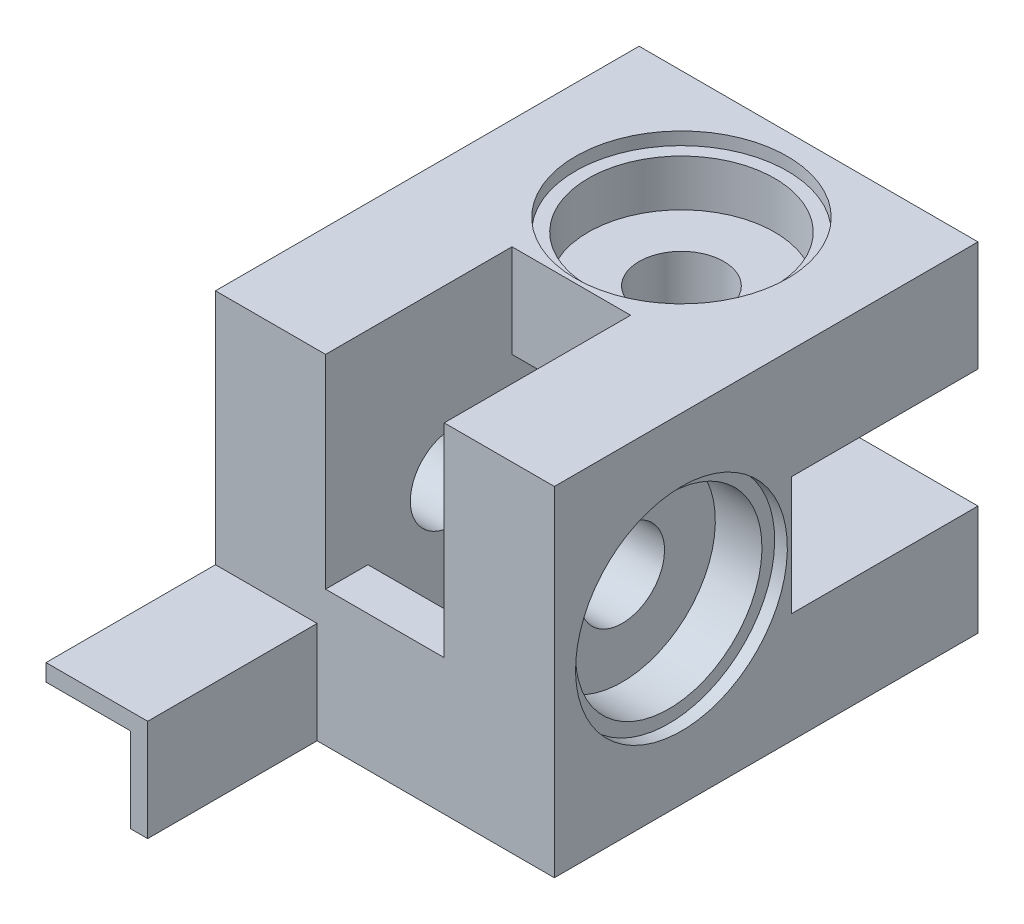
SolidWorks part; units mm, degrees
ref_plane "Plan de face" through (0, 0, 0) normal (0, 0, 1) x (1, 0, 0)
ref_plane "Plan de dessus" through (0, 0, 0) normal (0, 1, 0) x (1, 0, 0)
ref_plane "Plan de droite" through (0, 0, 0) normal (1, 0, 0) x (0, 0, -1)
sketch "Esquisse1" plane through (0, 0, 0) normal (0, 0, 1) x (1, 0, 0)
  line L1 (-40, 40) -> (0, 40)
  line L2 (-40, 40) -> (-40, 0)
  line L3 (-40, 0) -> (0, 0)
  line L4 (0, 40) -> (0, 0)
  dimension "D1" = 40
  dimension "D2" = 40
extrude "Boss.-Extru.1" add sketch "Esquisse1" along normal blind 50
sketch "Esquisse2" plane through (0, 40, 0) normal (0, 1, 0) x (1, 0, 0)
  line L0 (0, 0) -> (-40, 0) construction
  line L1 (-40, -50) -> (-40, 0) construction
  circle A0 centre (-20, -15) radius 5
  dimension "D1" = 10
  dimension "D2" = 15
  dimension "D3" = 20
extrude "Enlèv. mat.-Extru.1" cut sketch "Esquisse2" against normal through all
sketch "Esquisse3" plane through (-40, 0, 0) normal (-1, 0, 0) x (0, 0, 1)
  line L0 (50, 40) -> (50, 0) construction
  line L1 (50, 40) -> (0, 40) construction
  circle A0 centre (35, 20) radius 5
  dimension "D1" = 10
  dimension "D2" = 15
  dimension "D3" = 20
extrude "Enlèv. mat.-Extru.2" cut sketch "Esquisse3" against normal through all
sketch "Esquisse4" plane through (-40, 0, 0) normal (-1, 0, 0) x (0, 0, 1)
  line L1 (25, 27) -> (5, 27)
  line L2 (25, 27) -> (25, 13)
  line L3 (25, 13) -> (5, 13)
  line L4 (5, 27) -> (5, 13)
  line L5 (0, 40) -> (0, 0) construction
  line L6 (50, 0) -> (0, 0) construction
  line L7 (50, 40) -> (0, 40) construction
  dimension "D1" = 14
  dimension "D2" = 20
  dimension "D3" = 5
  dimension "D4" = 13
  dimension "D5" = 13
extrude "Enlèv. mat.-Extru.3" cut sketch "Esquisse4" against normal blind 29
sketch "Esquisse5" plane through (0, 0, 0) normal (0, -1, 0) x (1, 0, 0)
  line L0 (-40, 50) -> (0, 50) construction
  line L1 (-13, 25) -> (-27, 25)
  line L2 (-13, 25) -> (-13, 45)
  line L3 (-13, 45) -> (-27, 45)
  line L4 (-27, 25) -> (-27, 45)
  line L5 (-40, 50) -> (-40, 0) construction
  dimension "D1" = 20
  dimension "D2" = 5
  dimension "D3" = 14
  dimension "D4" = 13
extrude "Enlèv. mat.-Extru.4" cut sketch "Esquisse5" against normal blind 29
sketch "Esquisse6" plane through (0, 0, 0) normal (1, 0, 0) x (0, 0, -1)
  line L0 (0, 0) -> (0, 40) construction
  line L1 (0, 27) -> (-22, 27)
  line L2 (0, 27) -> (0, 13)
  line L3 (0, 13) -> (-22, 13)
  line L4 (-22, 27) -> (-22, 13)
  line L5 (-50, 0) -> (0, 0) construction
  dimension "D1" = 14
  dimension "D2" = 22
  dimension "D3" = 13
extrude "Enlèv. mat.-Extru.5" cut sketch "Esquisse6" against normal blind 24
sketch "Esquisse7" plane through (0, 40, 0) normal (0, 1, 0) x (1, 0, 0)
  line L0 (0, -50) -> (-40, -50) construction
  line L1 (-27, -50) -> (-13, -50)
  line L2 (-27, -50) -> (-27, -28)
  line L3 (-27, -28) -> (-13, -28)
  line L4 (-13, -50) -> (-13, -28)
  line L5 (-40, -50) -> (-40, 0) construction
  dimension "D1" = 14
  dimension "D2" = 22
  dimension "D3" = 13
extrude "Enlèv. mat.-Extru.6" cut sketch "Esquisse7" against normal blind 24
sketch "Esquisse8" plane through (0, 0, 0) normal (1, 0, 0) x (0, 0, -1)
  circle A0 centre (-35, 20) radius 11
  dimension "D1" = 22
extrude "Enlèv. mat.-Extru.7" cut sketch "Esquisse8" against normal blind 7
sketch "Esquisse9" plane through (0, 0, 0) normal (1, 0, 0) x (0, 0, -1)
  circle A0 centre (-35, 20) radius 12.5
  dimension "D1" = 25
extrude "Enlèv. mat.-Extru.8" cut sketch "Esquisse9" against normal blind 1.5
sketch "Esquisse10" plane through (0, 40, 0) normal (0, 1, 0) x (1, 0, 0)
  circle A0 centre (-20, -15) radius 11
  dimension "D1" = 22
extrude "Enlèv. mat.-Extru.9" cut sketch "Esquisse10" against normal blind 7
sketch "Esquisse11" plane through (0, 40, 0) normal (0, 1, 0) x (1, 0, 0)
  circle A0 centre (-20, -15) radius 12.5
  dimension "D1" = 25
extrude "Enlèv. mat.-Extru.10" cut sketch "Esquisse11" against normal blind 1.5
sketch "Esquisse13" plane through (0, 0, 50) normal (0, 0, 1) x (1, 0, 0)
  line L0 (-40, 10) -> (-30, 10)
  line L1 (-40, 40) -> (-40, 0) construction
  line L2 (-30, 10) -> (-30, 0)
  line L3 (-40, 0) -> (0, 0) construction
  line L4 (-30, 0) -> (-28, 0)
  line L5 (-28, 0) -> (-28, 12)
  line L6 (-28, 12) -> (-40, 12)
  line L7 (-40, 12) -> (-40, 10)
  dimension "D1" = 12
  dimension "D2" = 12
  dimension "D3" = 2
  dimension "D4" = 2
extrude "Boss.-Extru.2" add sketch "Esquisse13" along normal blind 20
